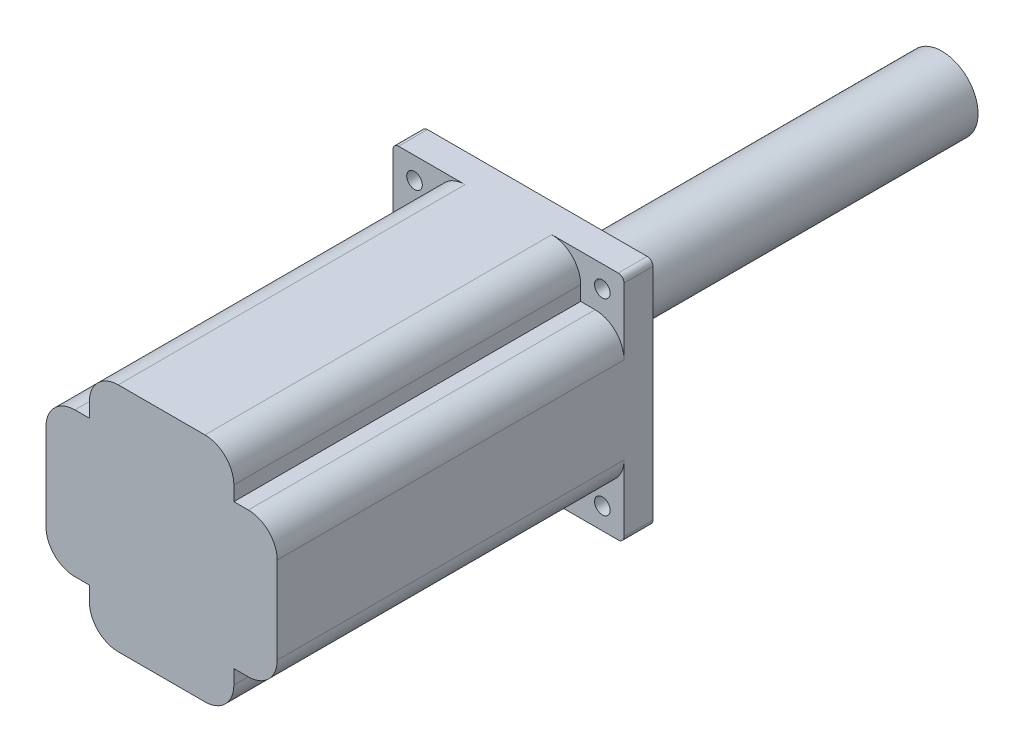
SolidWorks part; units mm, degrees
ref_plane "前视基准面" through (0, 0, 0) normal (0, 0, 1) x (1, 0, 0)
ref_plane "上视基准面" through (0, 0, 0) normal (0, 1, 0) x (1, 0, 0)
ref_plane "右视基准面" through (0, 0, 0) normal (1, 0, 0) x (0, 0, -1)
sketch "草图1" plane through (0, 0, 0) normal (0, 0, 1) x (1, 0, 0)
  line L0 (-136.3118, 0) -> (164.2586, 0) construction
  line L1 (-40, 40) -> (40, 40)
  line L2 (-40, 40) -> (-40, -40)
  line L3 (-40, -40) -> (40, -40)
  line L4 (40, 40) -> (40, -40)
  line L5 (-40, 40) -> (40, -40) construction
  line L6 (-40, -40) -> (40, 40) construction
  line L7 (0, 89.3541) -> (0, -97.1478) construction
  line L9 (-32.5, 32.5) -> (32.5, 32.5) construction
  line L10 (-32.5, 32.5) -> (-32.5, -32.5) construction
  line L11 (-32.5, -32.5) -> (32.5, -32.5) construction
  line L12 (32.5, 32.5) -> (32.5, -32.5) construction
  line L13 (-32.5, 32.5) -> (32.5, -32.5) construction
  line L14 (-32.5, -32.5) -> (32.5, 32.5) construction
  circle A0 centre (-32.5, 32.5) radius 2.7
  circle A1 centre (32.5, 32.5) radius 2.7
  circle A2 centre (32.5, -32.5) radius 2.7
  circle A3 centre (-32.5, -32.5) radius 2.7
  point P0 (0, 0)
  point P10 (0, 0)
  dimension "D3" = 65
  dimension "D1" = 80
  dimension "D2" = 80
extrude "凸台-拉伸1" add sketch "草图1" along normal blind 130
sketch "草图2" plane through (0, 0, 0) normal (0, 0, -1) x (-1, 0, 0)
  circle A0 centre (0, 0) radius 12.5
  dimension "D1" = 25
extrude "凸台-拉伸2" add sketch "草图2" along normal blind 140
sketch "草图3" plane through (0, 0, 130) normal (0, 0, 1) x (1, 0, 0)
  line L0 (-126.9071, 0) -> (137.1892, 0) construction
  line L1 (-40, 40) -> (-25, 40)
  line L2 (-40, 40) -> (-40, 25)
  line L3 (-40, 25) -> (-25, 25)
  line L4 (-25, 40) -> (-25, 25)
  line L5 (0, 116.4462) -> (0, -110.7211) construction
  line L6 (25, 40) -> (25, 25)
  line L7 (40, 25) -> (25, 25)
  line L8 (40, 40) -> (40, 25)
  line L9 (40, 40) -> (25, 40)
  line L10 (40, -40) -> (25, -40)
  line L11 (40, -40) -> (40, -25)
  line L12 (40, -25) -> (25, -25)
  line L13 (25, -40) -> (25, -25)
  line L14 (-25, -40) -> (-25, -25)
  line L15 (-40, -25) -> (-25, -25)
  line L16 (-40, -40) -> (-40, -25)
  line L17 (-40, -40) -> (-25, -40)
  dimension "D1" = 15
  dimension "D2" = 15
extrude "切除-拉伸1" cut sketch "草图3" against normal offset from surface (120 mm away) 10 up to face at (-12.5, 0, 0)
fillet "圆角1" radius 2 4 edges at (40, 40, 5) (40, -40, 5) (-40, 40, 5) (-40, -40, 5)
fillet "圆角3" radius 10 8 edges at (-40, -25, 70) (-25, -40, 70) (25, -40, 70) (40, -25, 70) (40, 25, 70) (25, 40, 70) (-40, 25, 70) (-25, 40, 70)
